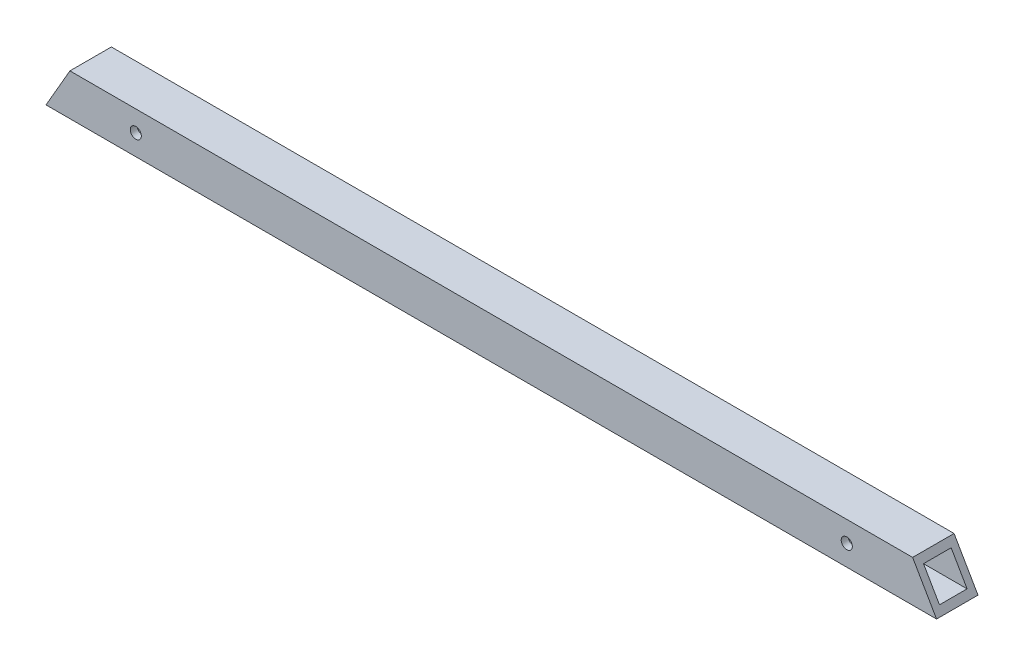
SolidWorks part; units mm, degrees
ref_plane "Front Plane" through (0, 0, 0) normal (0, 0, 1) x (1, 0, 0)
ref_plane "Top Plane" through (0, 0, 0) normal (0, 1, 0) x (1, 0, 0)
ref_plane "Right Plane" through (0, 0, 0) normal (1, 0, 0) x (0, 0, -1)
sketch "Sketch1" plane through (0, 0, 0) normal (1, 0, 0) x (0, 0, -1)
  line L0 (9.525, 15.875) -> (9.525, 19.05) construction
  line L1 (0, 0) -> (19.05, 0)
  line L2 (0, 0) -> (0, 19.05)
  line L3 (0, 19.05) -> (19.05, 19.05)
  line L4 (19.05, 0) -> (19.05, 19.05)
  line L5 (3.175, 3.175) -> (15.875, 3.175)
  line L6 (3.175, 3.175) -> (3.175, 15.875)
  line L7 (3.175, 15.875) -> (15.875, 15.875)
  line L8 (15.875, 3.175) -> (15.875, 15.875)
  line L10 (15.875, 9.525) -> (19.05, 9.525) construction
  dimension "D1" = 19.05
  dimension "D2" = 19.05
  dimension "D3" = 12.7
  dimension "D4" = 12.7
extrude "Boss-Extrude1" add sketch "Sketch1" along normal blind 431.8
sketch "Sketch2" plane through (0, 0, 0) normal (0, 0, 1) x (1, 0, 0)
  line L0 (0, 0) -> (10.9985, 19.05)
  line L1 (10.9985, 19.05) -> (10.9985, 0) construction
  line L2 (398.3485, 19.05) -> (398.3485, 0) construction
  line L3 (398.3485, 19.05) -> (409.347, 0)
  line L4 (0, 19.05) -> (0, 0)
  line L5 (0, 0) -> (431.8, 0)
  line L6 (431.8, 0) -> (431.8, 19.05)
  line L7 (431.8, 19.05) -> (0, 19.05)
  line L8 (0, 19.05) -> (0, 0)
  line L9 (0, 0) -> (431.8, 0)
  line L10 (431.8, 0) -> (431.8, 19.05)
  line L11 (431.8, 19.05) -> (0, 19.05)
  line M9 (0, 19.05) -> (0, 0)
  line M10 (0, 0) -> (431.8, 0)
  line M11 (431.8, 0) -> (431.8, 19.05)
  line M12 (431.8, 19.05) -> (0, 19.05)
  dimension "D2" = 30
  dimension "D3" = 30
  dimension "D4" = 387.35
  dimension "D1" = 0
extrude "Cut-Extrude1" cut sketch "Sketch2" against normal through all contours L3 M12 M10 M11 | L0 M9 M12
hole_wizard "#10 Clearance Hole1" positions "3DSketch1" profile "Sketch4" hole size "#10" standard "ANSI Inch" end condition through all
sketch3d "3DSketch1"
  line L0 (358.547, 19.05, 0) -> (358.547, 0, 0) construction
  line L1 (398.3485, 19.05, 0) -> (10.9985, 19.05, 0) construction
  line L2 (409.347, 0, 0) -> (0, 0, 0) construction
  line L4 (50.8, 19.05, 0) -> (50.8, 0, 0) construction
  line L5 (41.275, 9.525, 0) -> (50.8, 9.525, 0) construction
  line L7 (368.072, 9.525, 0) -> (358.547, 9.525, 0) construction
  point P0 (368.072, 9.525, 0)
  point P15 (41.275, 9.525, 0)
  dimension "D1" = 9.525
  dimension "D2" = 50.8
  dimension "D3" = 50.8
  dimension "D4" = 9.525
sketch "Sketch4" plane through (368.072, 9.525, 0) normal (1, 0, 0) x (0, -1, 0)
  line L0 (0, 0) -> (0, 19.05)
  line L1 (0, 19.05) -> (2.5527, 19.05)
  line L2 (2.5527, 19.05) -> (2.5527, 0)
  line L5 (2.5527, 0) -> (0, 0)
  line L11 (0, -6.35) -> (0, 107.95) construction
  dimension "Thru Hole Dia." = 5.1054
  dimension "Thru Hole Depth" = 19.05
